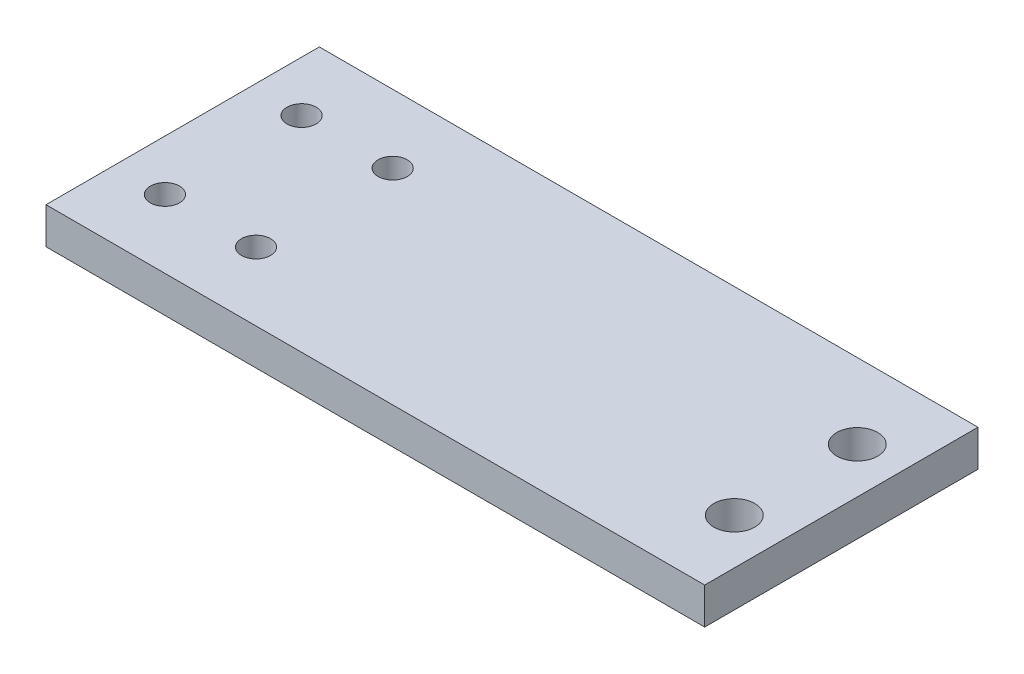
SolidWorks part; units mm, degrees
ref_plane "前视基准面" through (0, 0, 0) normal (0, 0, 1) x (1, 0, 0)
ref_plane "上视基准面" through (0, 0, 0) normal (0, 1, 0) x (1, 0, 0)
ref_plane "右视基准面" through (0, 0, 0) normal (1, 0, 0) x (0, 0, -1)
sketch "草图1" plane through (0, 0, 0) normal (0, 1, 0) x (1, 0, 0)
  line L0 (-27.7238, 7.998) -> (16.8491, 7.998) construction
  line L1 (16.8491, 7.998) -> (88.1064, 7.998) construction
  line L2 (48.5545, 22.998) -> (48.5545, -7.002)
  line L3 (48.5545, -7.002) -> (-23.7482, -7.002)
  line L4 (-23.7482, -7.002) -> (-23.7482, 22.998)
  line L5 (48.5545, 22.998) -> (-23.7482, 22.998)
  circle A0 centre (-18.1955, 15.498) radius 1.6
  circle A1 centre (-18.1955, 0.498) radius 1.6
  circle A2 centre (-8.1955, 15.498) radius 1.6
  circle A3 centre (-8.1955, 0.498) radius 1.6
  circle A4 centre (43.5545, 14.748) radius 2.25
  circle A5 centre (43.5545, 1.248) radius 2.25
  point P20 (48.5545, 7.998)
  point P21 (-23.7482, 7.998)
  dimension "D1" = 10
  dimension "D2" = 3.2
  dimension "D3" = 3.2
  dimension "D4" = 3.2
  dimension "D5" = 3.2
  dimension "D9" = 61.75
  dimension "D13" = 72.3027
  dimension "D6" = 15
  dimension "D7" = 7.5
  dimension "D8" = 7.5
  dimension "D10" = 6.75
  dimension "D11" = 5
  dimension "D12" = 15
extrude "凸台-拉伸1" add sketch "草图1" along normal blind 4
sketch "草图3" plane through (0, 4, 0) normal (0, 1, 0) x (1, 0, 0)
  line L0 (-8.1955, 15.498) -> (-8.1955, 0.498) construction
  line L1 (-8.1955, 7.998) -> (14.5156, 7.998) construction
sketch "草图4" plane through (0, 0, 0) normal (0, -1, 0) x (1, 0, 0)
  line L0 (-8.1955, -0.498) -> (-8.1955, -15.498) construction
  line L1 (-8.1955, -7.998) -> (17.1433, -7.998) construction
